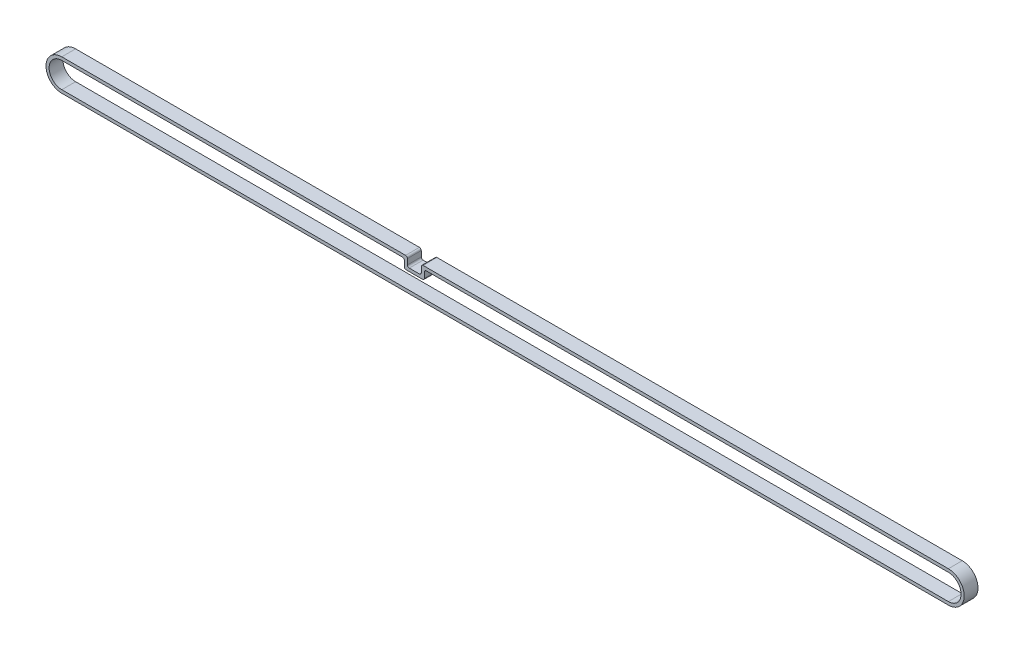
SolidWorks part; units mm, degrees
material "acero"
ref_plane "Alzado" through (0, 0, 0) normal (0, 0, 1) x (1, 0, 0)
ref_plane "Planta" through (0, 0, 0) normal (0, 1, 0) x (1, 0, 0)
ref_plane "Vista lateral" through (0, 0, 0) normal (1, 0, 0) x (0, 0, -1)
sketch "Croquis1" plane through (0, 0, 0) normal (0, 0, 1) x (1, 0, 0)
  line L0 (0, 0) -> (384.75, 0) construction
  line L1 (0, 5.5) -> (148.65, 5.5)
  line L2 (0, -5.5) -> (384.75, -5.5)
  line L3 (0, 6.85) -> (150, 6.85)
  line L4 (0, -6.85) -> (384.75, -6.85)
  line L5 (156, 2.85) -> (156, 6.85)
  line L6 (150, 2.85) -> (156, 2.85)
  line L7 (150, 2.85) -> (150, 6.85)
  line L8 (148.65, 5.5) -> (148.65, 1.5)
  line L9 (148.65, 1.5) -> (157.35, 1.5)
  line L10 (157.35, 1.5) -> (157.35, 5.5)
  line L11 (157.35, 5.5) -> (384.75, 5.5)
  line L12 (156, 6.85) -> (384.75, 6.85)
  line L13 (0, 5.5) -> (384.75, 5.5) construction
  line L15 (0, 6.85) -> (384.75, 6.85) construction
  arc A0 (0, 5.5) -> (0, -5.5) centre (0, 0) ccw
  arc A1 (384.75, 5.5) -> (384.75, -5.5) centre (384.75, 0) cw
  arc A2 (384.75, 6.85) -> (384.75, -6.85) centre (384.75, 0) cw
  arc A3 (0, 6.85) -> (0, -6.85) centre (0, 0) ccw
  point P21 (150, 4.85)
  dimension "D2" = 5.5
  dimension "D1" = 384.75
  dimension "D4" = 6
  dimension "D5" = 1.35
  dimension "D6" = 1.35
  dimension "D7" = 1.35
  dimension "D8" = 4
  dimension "D9" = 150
  dimension "D3" = 1.35
extrude "Saliente-Extruir1" add sketch "Croquis1" along normal blind 6
fillet "Redondeo1" radius 0.8 8 edges at (157.35, 5.5, 3) (148.65, 5.5, 3) (148.65, 1.5, 3) (156, 2.85, 3) (157.35, 1.5, 3) (156, 6.85, 3) (150, 6.85, 3) (150, 2.85, 3)
